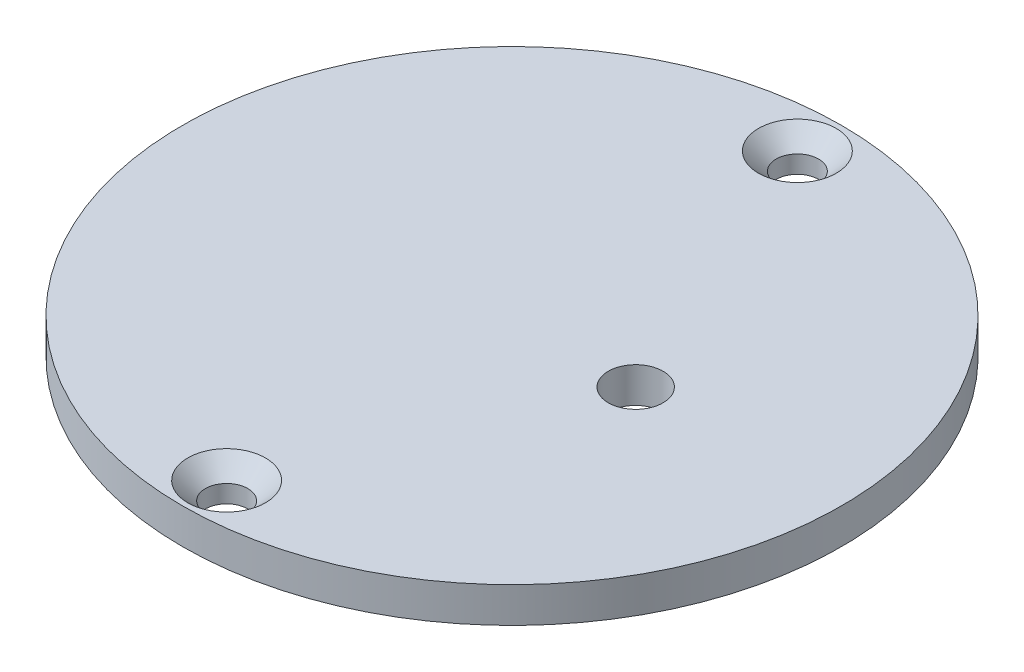
SolidWorks part; units mm, degrees
ref_plane "Спереди" through (0, 0, 0) normal (0, 0, 1) x (1, 0, 0)
ref_plane "Сверху" through (0, 0, 0) normal (0, 1, 0) x (1, 0, 0)
ref_plane "Справа" through (0, 0, 0) normal (1, 0, 0) x (0, 0, -1)
sketch "Эскиз1" plane through (0, 0, 0) normal (0, 1, 0) x (1, 0, 0)
  circle A0 centre (0, 0) radius 18.65
extrude "Бобышка-Вытянуть1" add sketch "Эскиз1" along normal blind 2
sketch "Эскиз2" plane through (0, 2, 0) normal (0, 1, 0) x (1, 0, 0)
  line L0 (0, 0) -> (7, 0) construction
  circle A0 centre (7, 0) radius 1.55
extrude "Вырез-Вытянуть1" cut sketch "Эскиз2" against normal blind 2
sketch "Эскиз3" plane through (0, 2, 0) normal (0, 1, 0) x (1, 0, 0)
  circle A0 centre (0, 0) radius 16.15 construction
  circle A1 centre (0, 16.15) radius 1.05
  circle A2 centre (0, -16.15) radius 1.05
hole_wizard "Зенковка для  винта с плоской головкой M21" positions "Эскиз5" profile "Эскиз4" countersink size "M2" standard "Ansi Metric" end condition through all
sketch "Эскиз5" plane through (0, 2, 0) normal (0, 1, 0) x (1, 0, 0)
  point P0 (0, 16.15)
  point P3 (0, -16.15)
sketch "Эскиз4" plane through (0, 2, -16.15) normal (1, 0, 0) x (0, 0, 1)
  line L0 (0, 0) -> (0, 2)
  line L1 (0, 2) -> (1.2, 2)
  line L2 (1.2, 2) -> (1.2, 1)
  line L3 (1.2, 1) -> (2.2, 0)
  line L5 (2.2, 0) -> (0, 0)
  line L6 (-1.2, 1) -> (-2.2, 0) construction
  line L11 (0, -6.35) -> (0, 107.95) construction
  dimension "Диаметр сквозного отверстия" = 2.4
  dimension "Глубина сквозного отверстия" = 2
  dimension "Диаметр передней зенковки" = 4.4
  dimension "Угол передней зенковки" = 90
